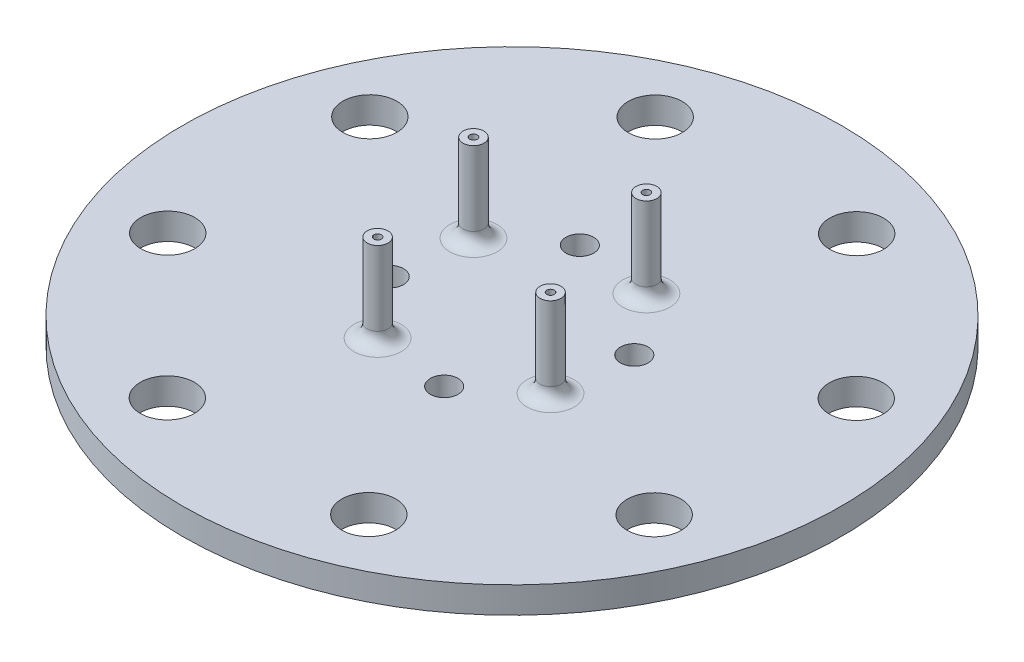
SolidWorks part; units mm, degrees
material "PTFE (general)"
ref_plane "Front Plane" through (0, 0, 0) normal (0, 0, 1) x (1, 0, 0)
ref_plane "Top Plane" through (0, 0, 0) normal (0, 1, 0) x (1, 0, 0)
ref_plane "Right Plane" through (0, 0, 0) normal (1, 0, 0) x (0, 0, -1)
sketch "Sketch1" plane through (0, 0, 0) normal (0, 1, 0) x (1, 0, 0)
  circle A0 centre (0, 0) radius 25
  dimension "D1" = 50
extrude "Boss-Extrude1" add sketch "Sketch1" along normal blind 2
sketch "Sketch2" plane through (0, 2, 0) normal (0, 1, 0) x (1, 0, 0)
  line L0 (0, 0) -> (2.0664, -7.2097) construction
  line L1 (0, 0) -> (-3.6369, -6.5592) construction
  circle A0 centre (0, 0) radius 7.5 construction
  circle A1 centre (-2.0664, 7.2097) radius 1.05
  circle A2 centre (7.2097, 2.0664) radius 1.05
  circle A3 centre (2.0664, -7.2097) radius 1.05
  circle A4 centre (-7.2097, -2.0664) radius 1.05
  circle A9 centre (-3.6369, -6.5592) radius 0.7938
  circle A10 centre (-6.5592, 3.6369) radius 0.7938
  circle A11 centre (3.6369, 6.5592) radius 0.7938
  circle A12 centre (6.5592, -3.6369) radius 0.7938
  point P21 (0, 0)
  point P23 (0, 0)
  dimension "D1" = 15
  dimension "D2" = 2.1
  dimension "D4" = 1.5875
  dimension "D5" = 45
  dimension "D3" = 4
  dimension "D6" = 4
extrude "Cut-Extrude1" cut sketch "Sketch2" against normal through all
sketch "Sketch3" [suppressed] plane through (0, 2, 0) normal (0, 1, 0) x (1, 0, 0)
  circle A0 centre (0, 0) radius 4
  circle A1 centre (0, 0) radius 17.5 construction
  circle A2 centre (17.0562, -3.9161) radius 4
  circle A3 centre (9.2915, -14.8296) radius 4
  circle A4 centre (-3.9161, -17.0562) radius 4
  circle A5 centre (-14.8296, -9.2915) radius 4
  circle A6 centre (-17.0562, 3.9161) radius 4
  circle A7 centre (-9.2915, 14.8296) radius 4
  circle A8 centre (3.9161, 17.0562) radius 4
  circle A9 centre (14.8296, 9.2915) radius 4
  point P23 (0, 0)
  dimension "D1" = 35
  dimension "8" = 8
  dimension "D2" = 8
  dimension "D3" = 8
ref_plane "Plane1" through (0, 0, -25) normal (0, 0, -1) x (-1, 0, 0)
sketch "Sketch4" plane through (0, 0, 0) normal (0, -1, 0) x (1, 0, 0)
  circle A0 centre (0, 0) radius 20 construction
  circle A5 centre (-18.4887, 7.6267) radius 2.05
  circle A6 centre (-18.4887, 7.6267) radius 2.05 construction
  circle A7 centre (-7.6806, 18.4664) radius 2.05
  circle A8 centre (7.6267, 18.4887) radius 2.05
  circle A9 centre (18.4664, 7.6806) radius 2.05
  circle A10 centre (18.4887, -7.6267) radius 2.05
  circle A11 centre (7.6806, -18.4664) radius 2.05
  circle A12 centre (-7.6267, -18.4887) radius 2.05
  circle A13 centre (-18.4664, -7.6806) radius 2.05
  point P31 (0, 0)
  dimension "D1" = 40
  dimension "D2" = 0
  dimension "D4" = 4.1
  dimension "D3" = 8
extrude "Cut-Extrude3" cut sketch "Sketch4" against normal through all
sketch "Sketch6" plane through (0, 0, 0) normal (0, -1, 0) x (1, 0, 0)
  circle A0 centre (20.3384, -6.9714) radius 1.55
  circle A1 centre (0, 0) radius 21.5 construction
  dimension "D1" = 3.1
  dimension "D2" = 43
extrude "Cut-Extrude4" [suppressed] cut sketch "Sketch6" against normal through all
sketch "Sketch7" plane through (0, 0, 0) normal (0, 1, 0) x (1, 0, 0)
  line L0 (0, 0) -> (-38.1181, 0) construction
  line L1 (0, 0) -> (0, -27.4458) construction
  line L2 (-3.6369, -6.5592) -> (-24.4617, -6.5592) construction
  line L3 (6.5592, -3.6369) -> (10.2973, -3.6369) construction
  line L4 (-6.5592, 3.6369) -> (11.0604, 3.6369) construction
  line L5 (3.6369, 6.5592) -> (10.2043, 6.5592) construction
  circle A0 centre (-3.6369, -6.5592) radius 0.7938
  circle A1 centre (-3.6369, -6.5592) radius 0.2858
  circle A2 centre (-6.5592, 3.6369) radius 0.2858
  circle A4 centre (6.5592, -3.6369) radius 0.7938
  circle A5 centre (6.5592, -3.6369) radius 0.2858
  circle A6 centre (-6.5592, 3.6369) radius 0.7938
  circle A7 centre (3.6369, 6.5592) radius 0.7938
  circle A8 centre (3.6369, 6.5592) radius 0.2858
  dimension "D1" = 1.5875
  dimension "D2" = 0.508
  dimension "D6" = 1.5875
  dimension "D7" = 0.508
  dimension "D8" = 1.5875
  dimension "D9" = 0.508
  dimension "D10" = 1.5875
  dimension "D11" = 0.508
  dimension "D3" = 3.6369
  dimension "D4" = 3.6369
  dimension "D5" = 2.9223
extrude "Boss-Extrude2" add sketch "Sketch7" along normal blind 8.64
fillet "Fillet1" radius 1 1 edges at (-6.5592, 2, -2.8432)
fillet "Fillet2" radius 1 1 edges at (-3.6369, 2, 7.3529)
fillet "Fillet3" radius 1 1 edges at (6.5592, 2, 4.4307)
fillet "Fillet4" radius 1 1 edges at (3.6369, 2, -5.7654)
